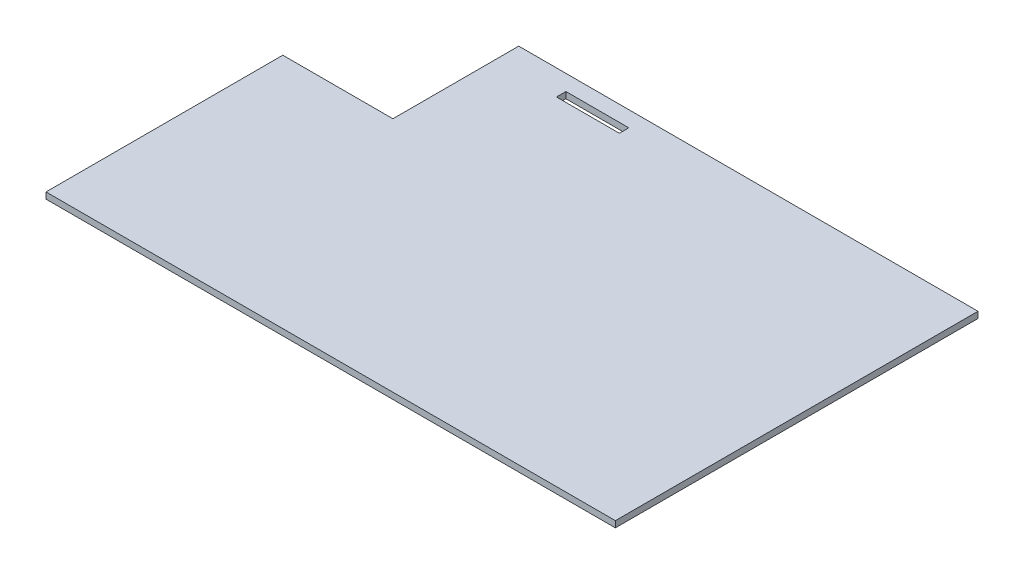
SolidWorks part; units mm, degrees
ref_plane "Front Plane" through (0, 0, 0) normal (0, 0, 1) x (1, 0, 0)
ref_plane "Top Plane" through (0, 0, 0) normal (0, 1, 0) x (1, 0, 0)
ref_plane "Right Plane" through (0, 0, 0) normal (1, 0, 0) x (0, 0, -1)
sketch "Sketch1" plane through (0, 0, 0) normal (0, 1, 0) x (1, 0, 0)
  line L0 (0, -50.8) -> (44.45, -50.8)
  line L1 (0, 0) -> (229.87, 0) construction
  line L2 (0, 0) -> (0, -146.4056) construction
  line L3 (0, -146.4056) -> (229.87, -146.4056)
  line L4 (229.87, 0) -> (229.87, -146.4056)
  line L5 (44.45, -50.8) -> (44.45, 0)
  line L6 (0, -146.4056) -> (0, -50.8)
  line L7 (69.85, -10.16) -> (95.25, -10.16)
  line L8 (69.85, -10.16) -> (69.85, -6.35)
  line L9 (69.85, -6.35) -> (95.25, -6.35)
  line L10 (95.25, -10.16) -> (95.25, -6.35)
  line L11 (44.45, 0) -> (229.87, 0)
  dimension "D1" = 229.87
  dimension "D2" = 146.4056
  dimension "D3" = 50.8
  dimension "D4" = 44.45
  dimension "D5" = 3.81
  dimension "D6" = 25.4
  dimension "D7" = 6.35
  dimension "D8" = 25.4
extrude "Boss-Extrude1" add sketch "Sketch1" along normal blind 2.54
